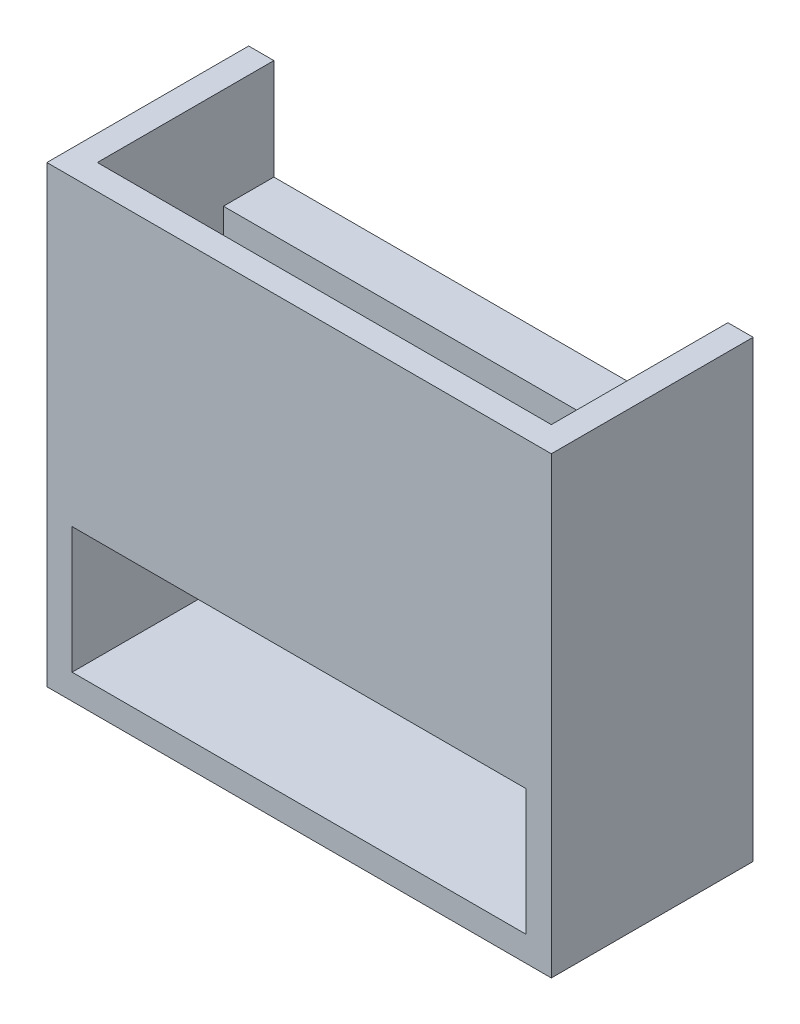
SolidWorks part; units mm, degrees
ref_plane "Front Plane" through (0, 0, 0) normal (0, 0, 1) x (1, 0, 0)
ref_plane "Top Plane" through (0, 0, 0) normal (0, 1, 0) x (1, 0, 0)
ref_plane "Right Plane" through (0, 0, 0) normal (1, 0, 0) x (0, 0, -1)
sketch "Sketch1" plane through (0, 0, 0) normal (0, 0, 1) x (1, 0, 0)
  line L1 (-10, 9) -> (10, 9)
  line L2 (-10, 9) -> (-10, -9)
  line L3 (-10, -9) -> (10, -9)
  line L4 (10, 9) -> (10, -9)
  line L5 (-10, 9) -> (10, -9) construction
  line L6 (-10, -9) -> (10, 9) construction
  point P0 (0, 0)
  dimension "D1" = 20
  dimension "D2" = 18
extrude "Boss-Extrude1" add sketch "Sketch1" along normal blind 8
sketch "Sketch2" plane through (0, 0, 8) normal (0, 0, 1) x (1, 0, 0)
  line L0 (-10, -9) -> (-9, -9)
  line L1 (-10, -9) -> (10, -9) construction
  line L2 (10, -9) -> (9, -9)
  line L3 (-10, -9) -> (-10, -4)
  line L4 (-10, 9) -> (-10, -9) construction
  line L5 (10, -9) -> (10, -8)
  line L7 (-9, -8) -> (9, -8)
  line L8 (-9, -8) -> (-9, -3)
  line L9 (-9, -3) -> (9, -3)
  line L10 (9, -8) -> (9, -3)
  dimension "D1" = 1
  dimension "D2" = 1
  dimension "D3" = 5
  dimension "D4" = 1
  dimension "D5" = 5
extrude "Cut-Extrude1" cut sketch "Sketch2" against normal blind 6 contours L7 L10 L9 L8
sketch "Sketch4" plane through (0, -3, 0) normal (0, -1, 0) x (1, 0, 0)
  line L0 (-9, 8) -> (-9, 7)
  line L1 (-9, 2) -> (-9, 8) construction
  line L3 (-9, 7) -> (9, 7)
  line L4 (-9, 7) -> (-9, 2)
  line L5 (-9, 2) -> (9, 2)
  line L6 (9, 7) -> (9, 2)
  line M3 (-9, 8) -> (-9, 2)
  line M4 (-9, 2) -> (9, 2)
  line M5 (9, 2) -> (9, 8)
  dimension "D1" = 1
extrude "Cut-Extrude2" cut sketch "Sketch4" against normal blind 13 contours L3 M3 M4 M5
sketch "Sketch5" plane through (0, 0, 0) normal (0, 0, -1) x (-1, 0, 0)
  line L0 (-10, 9) -> (-9, 9)
  line L1 (-10, 9) -> (10, 9) construction
  line L2 (10, 9) -> (9, 9)
  line L3 (10, 9) -> (10, -9) construction
  line L5 (-9, 9) -> (9, 9)
  line L6 (-9, 9) -> (-9, 5)
  line L7 (-9, 5) -> (9, 5)
  line L8 (9, 9) -> (9, 5)
  line M10 (10, 9) -> (-10, 9)
  dimension "D1" = 1
  dimension "D2" = 1
  dimension "D3" = 4
extrude "Cut-Extrude3" cut sketch "Sketch5" against normal blind 4 contours L8 L6 L7 M10
